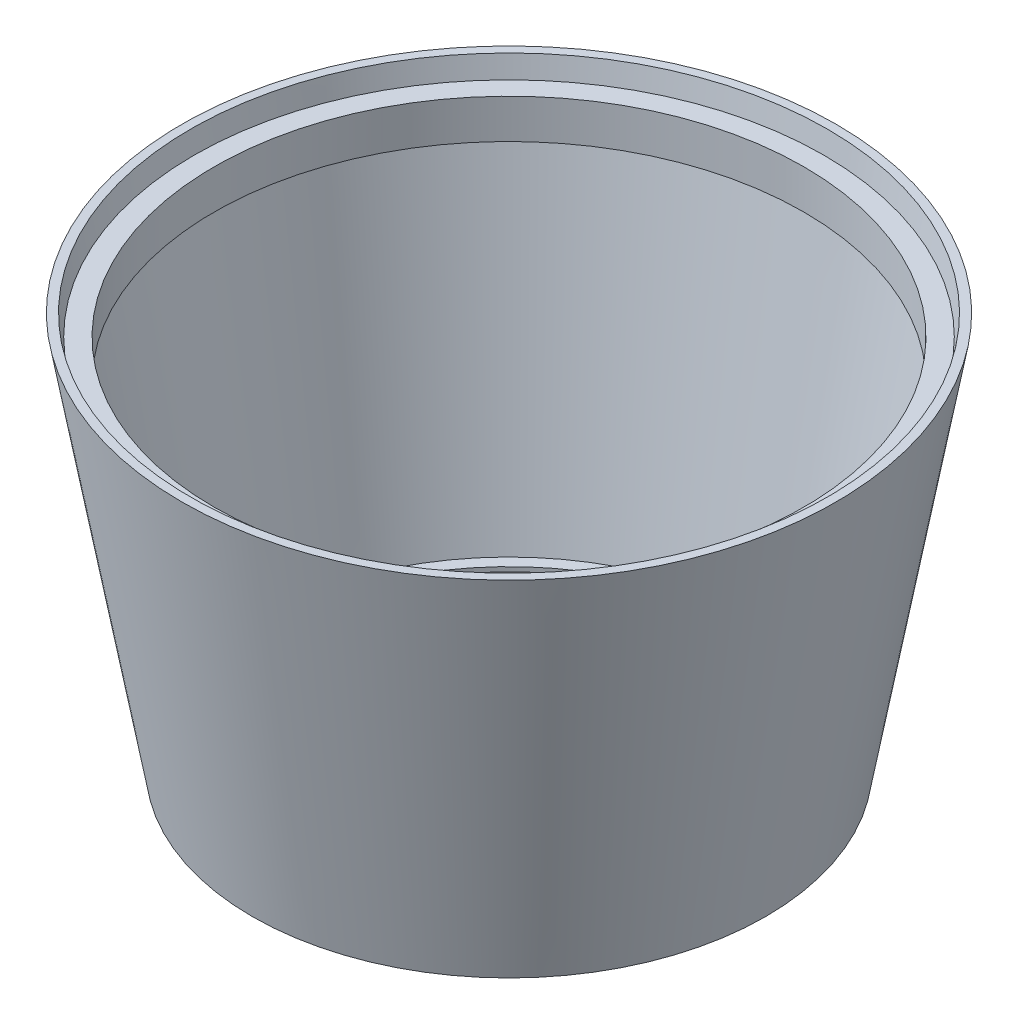
SolidWorks part; units mm, degrees
ref_plane "前视基准面" through (0, 0, 0) normal (0, 0, 1) x (1, 0, 0)
ref_plane "上视基准面" through (0, 0, 0) normal (0, 1, 0) x (1, 0, 0)
ref_plane "右视基准面" through (0, 0, 0) normal (1, 0, 0) x (0, 0, -1)
sketch "草图1" plane through (0, 0, 0) normal (0, 0, 1) x (1, 0, 0)
  line L0 (0, 0) -> (50, 0)
  line L1 (0, 0) -> (0, 14)
  line L2 (50, 0) -> (269.9221, 1231.6046)
  line L3 (269.9221, 1231.6046) -> (243.1418, 1231.6046)
  line L4 (243.1418, 1231.6046) -> (231.6099, 1167.0238)
  line L5 (231.6099, 1167.0238) -> (169.0441, 1167.0238)
  line L6 (169.0441, 1167.0238) -> (169.0441, 1044.4927)
  line L7 (220.7294, 1044.4927) -> (36.719, 14)
  line L8 (169.0441, 1044.4927) -> (220.7294, 1044.4927)
  line L9 (0, 14) -> (36.719, 14)
  line L10 (0, 0) -> (-752, 0) construction
  line L11 (-752, 0) -> (-752, 109.4948) construction
  point P3 (194.3995, 1059.3338)
  point P14 (269.9221, 1231.6046)
revolve "旋转1" add sketch "草图1" angle 360 about L11
